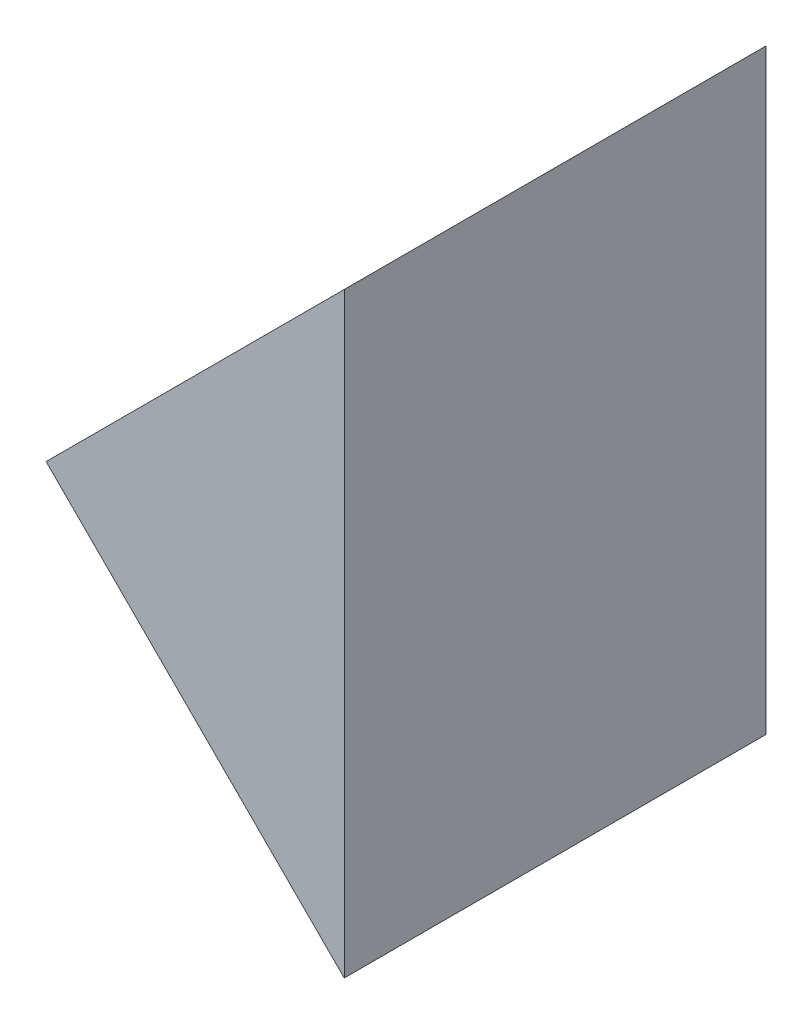
SolidWorks part; units mm, degrees
ref_plane "前视基准面" through (0, 0, 0) normal (0, 0, 1) x (1, 0, 0)
ref_plane "上视基准面" through (0, 0, 0) normal (0, 1, 0) x (1, 0, 0)
ref_plane "右视基准面" through (0, 0, 0) normal (1, 0, 0) x (0, 0, -1)
sketch "草图1" plane through (0, 0, 0) normal (0, 0, 1) x (1, 0, 0)
  line L0 (563.0072, 144.2705) -> (591.2915, 172.5548)
  line L1 (563.0072, 144.2705) -> (591.2915, 115.9862)
  line L2 (591.2915, 115.9862) -> (591.2915, 172.5548)
  dimension "D1" = 40
extrude "凸台-拉伸1" add sketch "草图1" along normal blind 40
